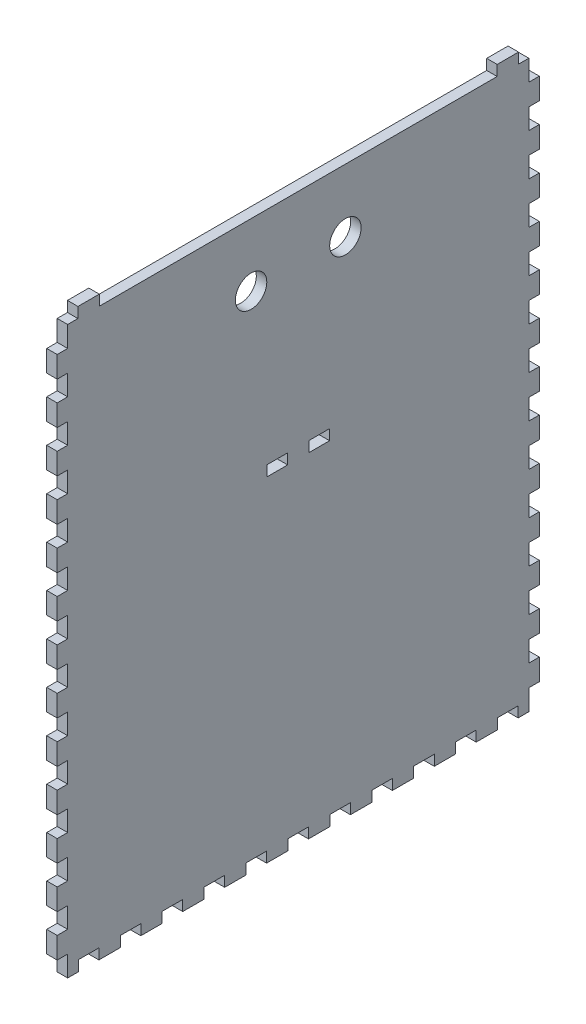
SolidWorks part; units mm, degrees
ref_plane "Front Plane" through (0, 0, 0) normal (0, 0, 1) x (1, 0, 0)
ref_plane "Top Plane" through (0, 0, 0) normal (0, 1, 0) x (1, 0, 0)
ref_plane "Right Plane" through (0, 0, 0) normal (1, 0, 0) x (0, 0, -1)
sketch "Sketch1" plane through (0, 0, 0) normal (1, 0, 0) x (0, 0, -1)
  line L0 (0, 0) -> (6.223, 0)
  line L1 (6.223, 0) -> (6.223, 6.35)
  line L2 (6.223, 6.35) -> (19.177, 6.35)
  line L3 (19.177, 6.35) -> (19.177, 0)
  line L4 (19.177, 0) -> (260.223, 0)
  line L5 (260.223, 0) -> (260.223, 6.35)
  line L6 (260.223, 6.35) -> (273.177, 6.35)
  line L7 (273.177, 6.35) -> (273.177, 0)
  line L8 (273.177, 0) -> (279.4, 0)
  line L9 (0, 0) -> (0, -12.573)
  line L10 (0, -12.573) -> (-6.35, -12.573)
  line L11 (-6.35, -12.573) -> (-6.35, -25.527)
  line L12 (-6.35, -25.527) -> (0, -25.527)
  line L13 (0, -25.527) -> (0, -37.973)
  line L14 (0, -37.973) -> (-6.35, -37.973)
  line L15 (-6.35, -37.973) -> (-6.35, -50.927)
  line L16 (-6.35, -50.927) -> (0, -50.927)
  line L17 (0, -50.927) -> (0, -63.373)
  line L18 (0, -63.373) -> (-6.35, -63.373)
  line L19 (-6.35, -63.373) -> (-6.35, -76.327)
  line L20 (-6.35, -76.327) -> (0, -76.327)
  line L21 (0, -76.327) -> (0, -88.773)
  line L22 (0, -88.773) -> (-6.35, -88.773)
  line L23 (-6.35, -88.773) -> (-6.35, -101.727)
  line L24 (-6.35, -101.727) -> (0, -101.727)
  line L25 (0, -101.727) -> (0, -114.173)
  line L26 (0, -114.173) -> (-6.35, -114.173)
  line L27 (-6.35, -114.173) -> (-6.35, -127.127)
  line L28 (-6.35, -127.127) -> (0, -127.127)
  line L29 (0, -127.127) -> (0, -139.573)
  line L30 (0, -139.573) -> (-6.35, -139.573)
  line L31 (-6.35, -139.573) -> (-6.35, -152.527)
  line L32 (-6.35, -152.527) -> (0, -152.527)
  line L33 (0, -152.527) -> (0, -164.973)
  line L34 (0, -164.973) -> (-6.35, -164.973)
  line L35 (-6.35, -164.973) -> (-6.35, -177.927)
  line L36 (-6.35, -177.927) -> (0, -177.927)
  line L37 (0, -177.927) -> (0, -190.373)
  line L38 (0, -190.373) -> (-6.35, -190.373)
  line L39 (-6.35, -190.373) -> (-6.35, -203.327)
  line L40 (-6.35, -203.327) -> (0, -203.327)
  line L41 (0, -203.327) -> (0, -215.773)
  line L42 (0, -215.773) -> (-6.35, -215.773)
  line L43 (-6.35, -215.773) -> (-6.35, -228.727)
  line L44 (-6.35, -228.727) -> (0, -228.727)
  line L45 (0, -228.727) -> (0, -241.173)
  line L46 (0, -241.173) -> (-6.35, -241.173)
  line L47 (-6.35, -241.173) -> (-6.35, -254.127)
  line L48 (-6.35, -254.127) -> (0, -254.127)
  line L49 (0, -254.127) -> (0, -266.573)
  line L50 (0, -266.573) -> (-6.35, -266.573)
  line L51 (-6.35, -266.573) -> (-6.35, -279.527)
  line L52 (-6.35, -279.527) -> (0, -279.527)
  line L53 (0, -279.527) -> (0, -291.973)
  line L54 (279.4, -330.327) -> (279.4, -342.9)
  line L55 (-6.35, -330.327) -> (0, -330.327)
  line L56 (0, -291.973) -> (-6.35, -291.973)
  line L57 (-6.35, -291.973) -> (-6.35, -304.927)
  line L58 (-6.35, -304.927) -> (0, -304.927)
  line L59 (0, -342.9) -> (6.477, -342.9)
  line L60 (0, -304.927) -> (0, -317.373)
  line L61 (0, -317.373) -> (-6.35, -317.373)
  line L62 (-6.35, -317.373) -> (-6.35, -330.327)
  line L76 (0, -330.327) -> (0, -342.9)
  line L88 (285.75, -330.327) -> (279.4, -330.327)
  line L89 (285.75, -317.373) -> (285.75, -330.327)
  line L90 (279.4, -317.373) -> (285.75, -317.373)
  line L91 (279.4, -304.927) -> (279.4, -317.373)
  line L92 (285.75, -304.927) -> (279.4, -304.927)
  line L93 (285.75, -291.973) -> (285.75, -304.927)
  line L94 (279.4, -291.973) -> (285.75, -291.973)
  line L95 (279.4, -279.527) -> (279.4, -291.973)
  line L96 (285.75, -279.527) -> (279.4, -279.527)
  line L97 (285.75, -266.573) -> (285.75, -279.527)
  line L98 (279.4, -266.573) -> (285.75, -266.573)
  line L99 (279.4, -254.127) -> (279.4, -266.573)
  line L100 (285.75, -254.127) -> (279.4, -254.127)
  line L101 (285.75, -241.173) -> (285.75, -254.127)
  line L102 (279.4, -241.173) -> (285.75, -241.173)
  line L103 (279.4, -228.727) -> (279.4, -241.173)
  line L104 (285.75, -228.727) -> (279.4, -228.727)
  line L105 (285.75, -215.773) -> (285.75, -228.727)
  line L106 (279.4, -215.773) -> (285.75, -215.773)
  line L107 (279.4, -203.327) -> (279.4, -215.773)
  line L108 (285.75, -203.327) -> (279.4, -203.327)
  line L109 (285.75, -190.373) -> (285.75, -203.327)
  line L110 (139.7, 0) -> (139.7, -304.927) construction
  line L111 (279.4, -190.373) -> (285.75, -190.373)
  line L112 (133.2865, -133.985) -> (133.2865, -140.335)
  line L113 (279.4, -177.927) -> (279.4, -190.373)
  line L114 (285.75, -177.927) -> (279.4, -177.927)
  line L115 (285.75, -164.973) -> (285.75, -177.927)
  line L116 (279.4, -164.973) -> (285.75, -164.973)
  line L117 (279.4, -152.527) -> (279.4, -164.973)
  line L118 (285.75, -152.527) -> (279.4, -152.527)
  line L119 (285.75, -139.573) -> (285.75, -152.527)
  line L120 (279.4, -139.573) -> (285.75, -139.573)
  line L121 (279.4, -127.127) -> (279.4, -139.573)
  line L122 (285.75, -127.127) -> (279.4, -127.127)
  line L123 (285.75, -114.173) -> (285.75, -127.127)
  line L124 (279.4, -114.173) -> (285.75, -114.173)
  line L125 (279.4, -101.727) -> (279.4, -114.173)
  line L126 (285.75, -101.727) -> (279.4, -101.727)
  line L127 (285.75, -88.773) -> (285.75, -101.727)
  line L128 (279.4, -88.773) -> (285.75, -88.773)
  line L129 (279.4, -76.327) -> (279.4, -88.773)
  line L130 (285.75, -76.327) -> (279.4, -76.327)
  line L131 (285.75, -63.373) -> (285.75, -76.327)
  line L132 (279.4, -63.373) -> (285.75, -63.373)
  line L133 (279.4, -50.927) -> (279.4, -63.373)
  line L134 (285.75, -50.927) -> (279.4, -50.927)
  line L135 (285.75, -37.973) -> (285.75, -50.927)
  line L136 (279.4, -37.973) -> (285.75, -37.973)
  line L137 (279.4, -25.527) -> (279.4, -37.973)
  line L138 (285.75, -25.527) -> (279.4, -25.527)
  line L139 (285.75, -12.573) -> (285.75, -25.527)
  line L140 (279.4, -12.573) -> (285.75, -12.573)
  line L141 (279.4, 0) -> (279.4, -12.573)
  line L161 (158.6865, -133.985) -> (146.1135, -133.985)
  line L162 (158.6865, -133.985) -> (158.6865, -140.335)
  line L163 (158.6865, -140.335) -> (146.1135, -140.335)
  line L164 (146.1135, -133.985) -> (146.1135, -140.335)
  line L165 (120.7135, -140.335) -> (133.2865, -140.335)
  line L166 (120.7135, -133.985) -> (120.7135, -140.335)
  line L167 (120.7135, -133.985) -> (133.2865, -133.985)
  line L194 (6.477, -342.9) -> (6.477, -336.55)
  line L195 (6.477, -336.55) -> (18.923, -336.55)
  line L196 (18.923, -336.55) -> (18.923, -342.9)
  line L197 (18.923, -342.9) -> (31.877, -342.9)
  line L198 (31.877, -342.9) -> (31.877, -336.55)
  line L199 (31.877, -336.55) -> (44.323, -336.55)
  line L200 (44.323, -336.55) -> (44.323, -342.9)
  line L201 (44.323, -342.9) -> (57.277, -342.9)
  line L202 (57.277, -342.9) -> (57.277, -336.55)
  line L203 (57.277, -336.55) -> (69.723, -336.55)
  line L204 (69.723, -336.55) -> (69.723, -342.9)
  line L205 (69.723, -342.9) -> (82.677, -342.9)
  line L206 (82.677, -342.9) -> (82.677, -336.55)
  line L207 (82.677, -336.55) -> (95.123, -336.55)
  line L208 (95.123, -336.55) -> (95.123, -342.9)
  line L209 (95.123, -342.9) -> (108.077, -342.9)
  line L210 (108.077, -342.9) -> (108.077, -336.55)
  line L211 (108.077, -336.55) -> (120.523, -336.55)
  line L212 (120.523, -336.55) -> (120.523, -342.9)
  line L213 (120.523, -342.9) -> (133.477, -342.9)
  line L214 (133.477, -342.9) -> (133.477, -336.55)
  line L215 (133.477, -336.55) -> (145.923, -336.55)
  line L216 (145.923, -336.55) -> (145.923, -342.9)
  line L217 (145.923, -342.9) -> (158.877, -342.9)
  line L218 (158.877, -342.9) -> (158.877, -336.55)
  line L219 (158.877, -336.55) -> (171.323, -336.55)
  line L220 (171.323, -336.55) -> (171.323, -342.9)
  line L221 (171.323, -342.9) -> (184.277, -342.9)
  line L222 (184.277, -342.9) -> (184.277, -336.55)
  line L223 (184.277, -336.55) -> (196.723, -336.55)
  line L224 (196.723, -336.55) -> (196.723, -342.9)
  line L225 (196.723, -342.9) -> (209.677, -342.9)
  line L226 (209.677, -342.9) -> (209.677, -336.55)
  line L227 (209.677, -336.55) -> (222.123, -336.55)
  line L228 (222.123, -336.55) -> (222.123, -342.9)
  line L229 (222.123, -342.9) -> (235.077, -342.9)
  line L230 (235.077, -342.9) -> (235.077, -336.55)
  line L231 (235.077, -336.55) -> (247.523, -336.55)
  line L232 (247.523, -336.55) -> (247.523, -342.9)
  line L233 (247.523, -342.9) -> (260.477, -342.9)
  line L234 (260.477, -342.9) -> (260.477, -336.55)
  line L235 (260.477, -336.55) -> (272.923, -336.55)
  line L236 (272.923, -336.55) -> (272.923, -342.9)
  line L237 (272.923, -342.9) -> (279.4, -342.9)
  line L238 (272.923, -342.9) -> (285.877, -342.9) [skipped]
  line L275 (0, -330.327) -> (0, -342.773) [skipped]
  line L276 (-6.35, -330.327) -> (0, -330.327) [skipped]
  circle A0 centre (111.125, -38.1) radius 9.525
  circle A1 centre (168.275, -38.1) radius 9.525
  dimension "D15" = 19.05
  dimension "D2" = 6.35
  dimension "D3" = 6.35
  dimension "D4" = 6.223
  dimension "D5" = 12.954
  dimension "D6" = 6.477
  dimension "D7" = 241.046
  dimension "D8" = 12.954
  dimension "D9" = 12.573
  dimension "D10" = 6.35
  dimension "D11" = 12.446
  dimension "D13" = 133.985
  dimension "D14" = 12.573
  dimension "D16" = 38.1
  dimension "D17" = 28.575
  dimension "D19" = 12.446
  dimension "D21" = 12.954
  dimension "D22" = 12.573
  dimension "D23" = 6.35
  dimension "D24" = 6.4135
  dimension "D25" = 6.35
  dimension "D26" = 6.35
  dimension "D27" = 11
  dimension "D28" = 6.477
  dimension "D12" = 13
extrude "Boss-Extrude1" add sketch "Sketch1" along normal blind 6.35
